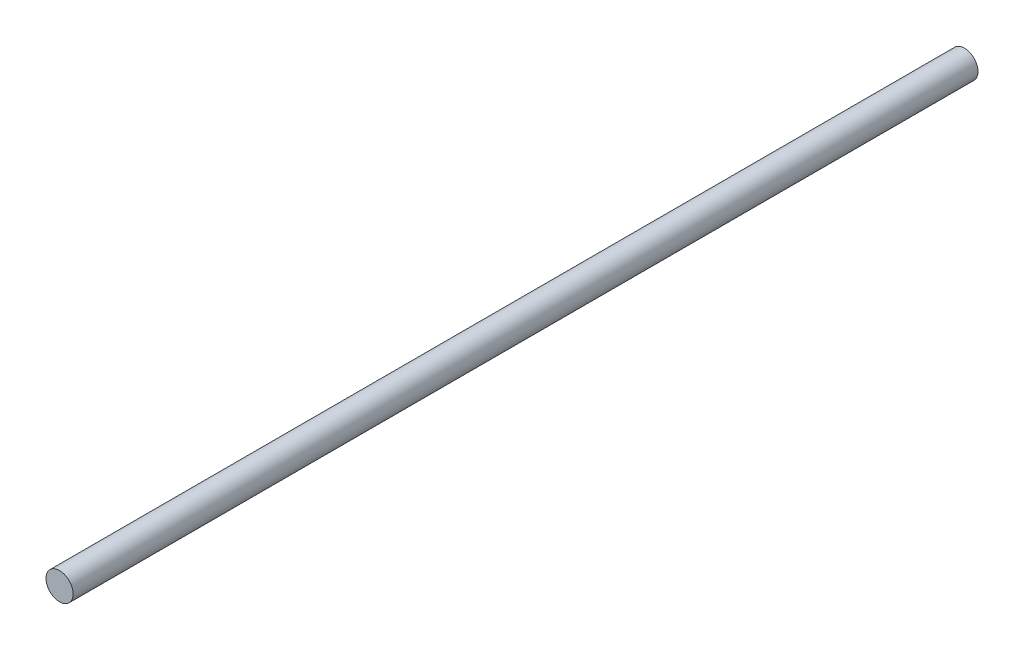
SolidWorks part; units mm, degrees
material "АД 31 ГОСТ 4784-97"
ref_plane "Plane1" through (0, 0, 0) normal (0, 0, 1) x (1, 0, 0)
ref_plane "Plane2" through (0, 0, 0) normal (0, 1, 0) x (1, 0, 0)
ref_plane "Plane3" through (0, 0, 0) normal (1, 0, 0) x (0, 0, -1)
sketch "Эскиз1" plane through (0, 0, 0) normal (0, 0, 1) x (1, 0, 0)
  circle A0 centre (0, 0) radius 3
  dimension "D1" = 6
extrude "Бобышка-Вытянуть1" add sketch "Эскиз1" along normal blind 200
